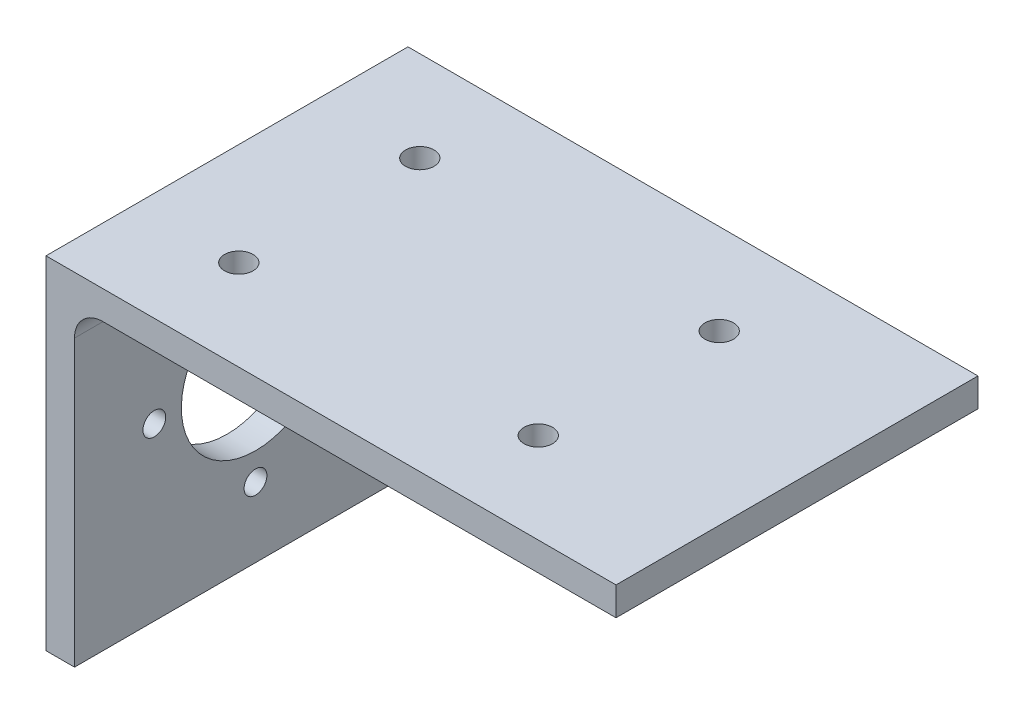
SolidWorks part; units mm, degrees
ref_plane "Front Plane" through (0, 0, 0) normal (0, 0, 1) x (1, 0, 0)
ref_plane "Top Plane" through (0, 0, 0) normal (0, 1, 0) x (1, 0, 0)
ref_plane "Right Plane" through (0, 0, 0) normal (1, 0, 0) x (0, 0, -1)
sketch "Sketch1" plane through (0, 0, 0) normal (0, 0, 1) x (1, 0, 0)
  line L0 (-108.5502, 0) -> (108.5502, 0) construction
  line L1 (0, 113.7546) -> (0, -113.7546) construction
  line L2 (0, 0) -> (0, 60)
  line L3 (0, 60) -> (100, 60)
  line L4 (100, 60) -> (100, 55)
  line L5 (100, 55) -> (10, 55)
  line L6 (5, 50) -> (5, 0)
  line L7 (5, 0) -> (0, 0)
  arc A0 (10, 55) -> (5, 50) centre (10, 50) ccw
  point P5 (0, 0)
  point P6 (0, 0)
  dimension "D5" = 5
  dimension "D1" = 100
  dimension "D2" = 60
  dimension "D3" = 5
  dimension "D4" = 5
extrude "Boss-Extrude1" add sketch "Sketch1" along normal blind 63.5
sketch "Sketch2" plane through (0, 0, 0) normal (-1, 0, 0) x (0, 0, 1)
  line L0 (0, 30) -> (63.5, 30) construction
  line L1 (0, 60) -> (0, 0) construction
  line L2 (63.5, 60) -> (63.5, 0) construction
  line L4 (63.5, 60) -> (0, 60) construction
  line L5 (31.75, 60) -> (31.75, 0) construction
  line L6 (63.5, 0) -> (0, 0) construction
  circle A0 centre (31.75, 30) radius 13
  circle A2 centre (49.5, 30) radius 2
  circle A3 centre (31.75, 12.25) radius 2
  circle A4 centre (14, 30) radius 2
  circle A5 centre (31.75, 47.75) radius 2
  dimension "D1" = 26
  dimension "D2" = 4
  dimension "D3" = 17.75
  dimension "D4" = 4
extrude "Cut-Extrude1" cut sketch "Sketch2" against normal blind 5
sketch "Sketch3" plane through (0, 60, 0) normal (0, 1, 0) x (1, 0, 0)
  line L0 (50, 0) -> (50, -63.5) construction
  line L1 (100, 0) -> (0, 0) construction
  line L2 (100, -63.5) -> (0, -63.5) construction
  line L3 (0, -31.75) -> (100, -31.75) construction
  line L4 (0, -63.5) -> (0, 0) construction
  line L5 (100, -63.5) -> (100, 0) construction
  circle A4 centre (23.735, -15.875) radius 2.5
  circle A5 centre (76.265, -15.875) radius 2.5
  circle A6 centre (76.265, -47.625) radius 2.5
  circle A7 centre (23.735, -47.625) radius 2.5
  point P14 (50, -31.75)
  dimension "D2" = 52.53
  dimension "D1" = 5
  dimension "D3" = 15.875
sketch "Sketch4" plane through (0, 60, 0) normal (0, 1, 0) x (1, 0, 0)
  line L0 (100, -31.75) -> (0, -31.75) construction
  line L1 (100, -63.5) -> (100, 0) construction
  line L2 (0, -63.5) -> (0, 0) construction
  line L3 (50, 0) -> (50, -63.5) construction
  line L4 (100, 0) -> (0, 0) construction
  line L5 (100, -63.5) -> (0, -63.5) construction
  circle A0 centre (70.4798, -47.625) radius 2.5
  circle A1 centre (17.9498, -47.625) radius 2.5
  circle A2 centre (17.9498, -15.875) radius 2.5
  circle A3 centre (70.4798, -15.875) radius 2.5
  dimension "D1" = 5
  dimension "D2" = 31.75
  dimension "D3" = 52.53
extrude "Cut-Extrude3" cut sketch "Sketch4" against normal blind 10
